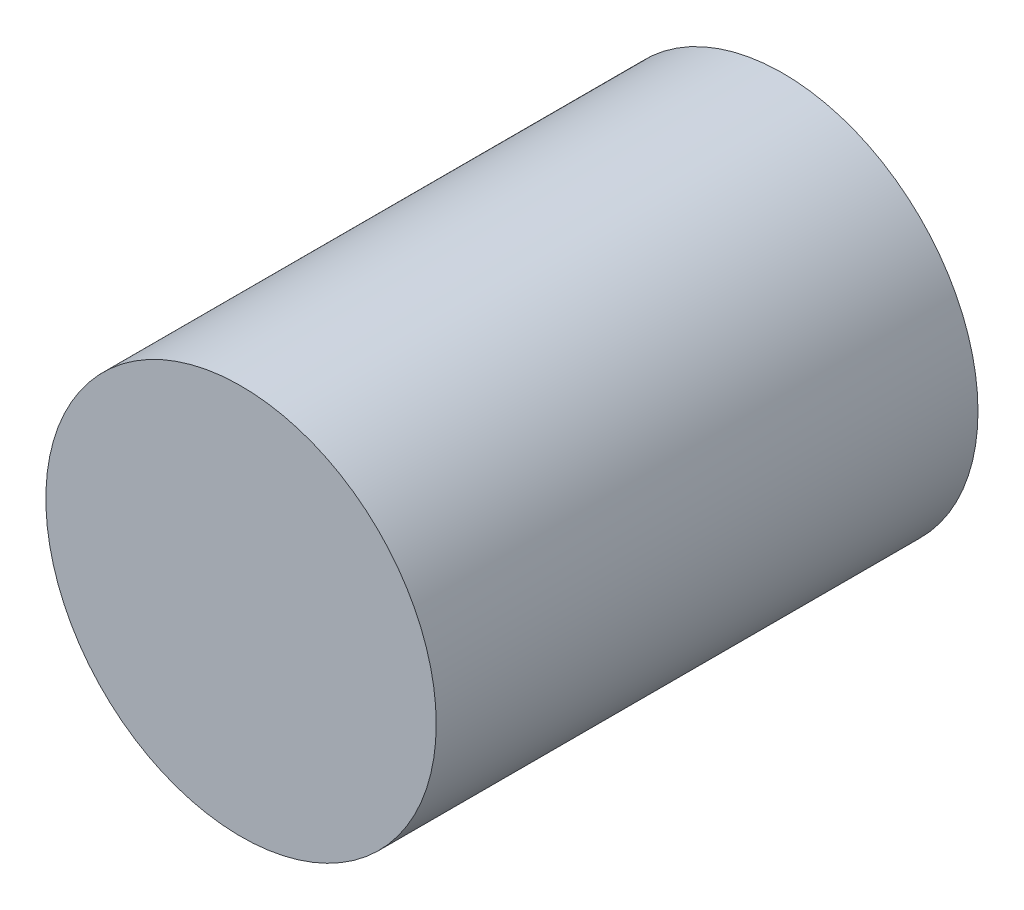
SolidWorks part; units mm, degrees
material "AISI Type 316L stainless steel"
ref_plane "Front Plane" through (0, 0, 0) normal (0, 0, 1) x (1, 0, 0)
ref_plane "Top Plane" through (0, 0, 0) normal (0, 1, 0) x (1, 0, 0)
ref_plane "Right Plane" through (0, 0, 0) normal (1, 0, 0) x (0, 0, -1)
sketch "Sketch1" plane through (0, 0, 0) normal (0, 0, 1) x (1, 0, 0)
  circle A0 centre (0, 0) radius 9.7231
  dimension "D1" = 19.4462
extrude "Boss-Extrude1" add sketch "Sketch1" along normal mid plane 26.9875
